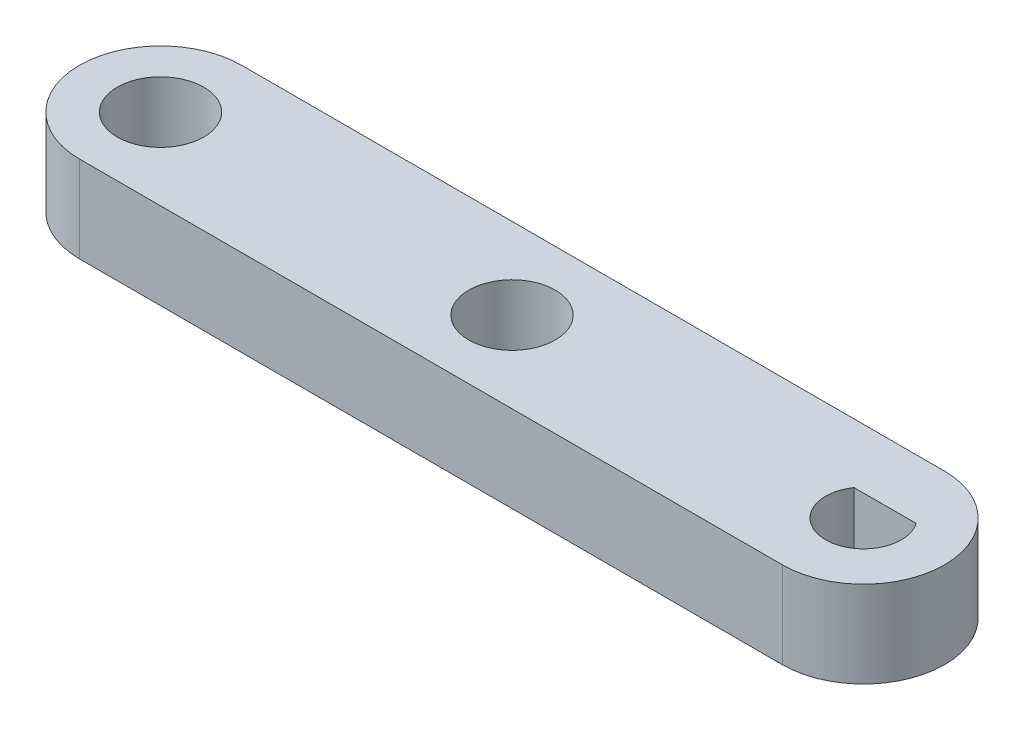
SolidWorks part; units mm, degrees
ref_plane "Front Plane" through (0, 0, 0) normal (0, 0, 1) x (1, 0, 0)
ref_plane "Top Plane" through (0, 0, 0) normal (0, 1, 0) x (1, 0, 0)
ref_plane "Right Plane" through (0, 0, 0) normal (1, 0, 0) x (0, 0, -1)
sketch "Sketch1" plane through (0, 0, 0) normal (0, 1, 0) x (1, 0, 0)
  line L0 (0, 0) -> (32.5, 0) construction
  line L1 (0, 3.75) -> (32.5, 3.75)
  line L2 (0, -3.75) -> (32.5, -3.75)
  line L3 (-2, 0) -> (-3.75, 0) construction
  line L4 (34.5, 0) -> (36.25, 0) construction
  line L5 (31.0639, 1) -> (33.9361, 1)
  line L6 (32.5, 1) -> (32.5, -1.75) construction
  arc A0 (0, 3.75) -> (0, -3.75) centre (0, 0) ccw
  arc A1 (32.5, -3.75) -> (32.5, 3.75) centre (32.5, 0) ccw
  circle A2 centre (0, 0) radius 2
  circle A3 centre (16.25, 0) radius 2
  circle A4 centre (32.5, 0) radius 2 construction
  circle A5 centre (32.5, 0) radius 1.75 construction
  arc A6 (31.0639, 1) -> (33.9361, 1) centre (32.5, 0) ccw
  point P3 (16.25, 0)
  dimension "D1" = 4
  dimension "D4" = 3.5
  dimension "D2" = 40
  dimension "D3" = 7.5
  dimension "D5" = 2.75
extrude "Boss-Extrude1" add sketch "Sketch1" along normal blind 4
